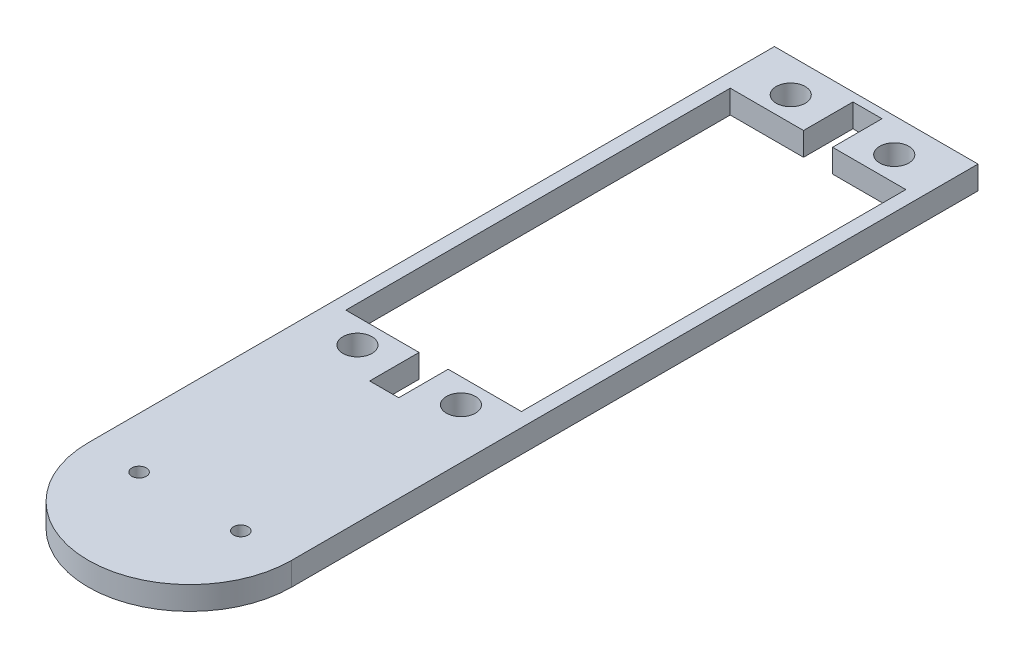
SolidWorks part; units mm, degrees
ref_plane "Front Plane" through (0, 0, 0) normal (0, 0, 1) x (1, 0, 0)
ref_plane "Top Plane" through (0, 0, 0) normal (0, 1, 0) x (1, 0, 0)
ref_plane "Right Plane" through (0, 0, 0) normal (1, 0, 0) x (0, 0, -1)
sketch "Sketch1" plane through (0, 0, 0) normal (0, 1, 0) x (1, 0, 0)
  line L0 (-17.5, 0) -> (-17.5, 118)
  line L1 (-17.5, 118) -> (17.5, 118)
  line L2 (17.5, 118) -> (17.5, 0)
  arc A0 (-17.5, 0) -> (17.5, 0) centre (0, 0) ccw
extrude "Boss-Extrude1" add sketch "Sketch1" along normal blind 4
sketch "Sketch2" plane through (0, 4, 0) normal (0, 1, 0) x (1, 0, 0)
  line L0 (-17.5, 0) -> (0, 0) construction
  line L1 (0, 0) -> (17.5, 0) construction
  circle A0 centre (-8.75, 0) radius 1.25
  circle A1 centre (8.75, 0) radius 1.25
extrude "Cut-Extrude1" cut sketch "Sketch2" against normal blind 4
sketch "Sketch6" plane through (0, 4, 0) normal (0, 1, 0) x (1, 0, 0)
  line L0 (-17.5, 118) -> (-15.1, 118) construction
  line L1 (17.5, 118) -> (-17.5, 118) construction
  line L2 (-15.1, 118) -> (-15.1, 108) construction
  line L3 (-15.1, 74.95) -> (15.1, 74.95) construction
  line L4 (-15.1, 108) -> (15.1, 108)
  line L5 (-15.1, 108) -> (-15.1, 41.9)
  line L6 (-15.1, 41.9) -> (15.1, 41.9)
  line L7 (15.1, 108) -> (15.1, 41.9)
  line L9 (-17.5, 118) -> (-17.5, 0) construction
  line L10 (0, 41.9) -> (0, 31.7405) construction
  circle A0 centre (-8.9, 37.7) radius 2.5
  circle A1 centre (8.9, 37.7) radius 2.5
  circle A2 centre (8.9, 112.2) radius 2.5
  circle A3 centre (-8.9, 112.2) radius 2.5
  dimension "D3" = 8.6
  dimension "D1" = 66.1
  dimension "D2" = 30.2
  dimension "D4" = 4.2
extrude "Cut-Extrude5" cut sketch "Sketch6" against normal blind 4
sketch "Sketch7" plane through (0, 4, 0) normal (0, 1, 0) x (1, 0, 0)
  line L0 (0, 41.9) -> (0, 22.9123) construction
  line L1 (-15.1, 41.9) -> (15.1, 41.9) construction
  line L2 (0, 41.9) -> (-2.5, 41.9)
  line L3 (-2.5, 41.9) -> (-2.5, 33.4)
  line L4 (-2.5, 33.4) -> (2.5, 33.4)
  line L5 (2.5, 33.4) -> (2.5, 41.9)
  line L6 (2.5, 41.9) -> (0, 41.9)
  line L7 (15.1, 74.95) -> (-15.1, 74.95) construction
  line L8 (15.1, 41.9) -> (15.1, 108) construction
  line L9 (-15.1, 108) -> (-15.1, 41.9) construction
  line L10 (2.5, 108) -> (0, 108)
  line L11 (2.5, 116.5) -> (2.5, 108)
  line L12 (-2.5, 116.5) -> (2.5, 116.5)
  line L13 (-2.5, 108) -> (-2.5, 116.5)
  line L14 (0, 108) -> (-2.5, 108)
extrude "Cut-Extrude6" cut sketch "Sketch7" against normal blind 4
